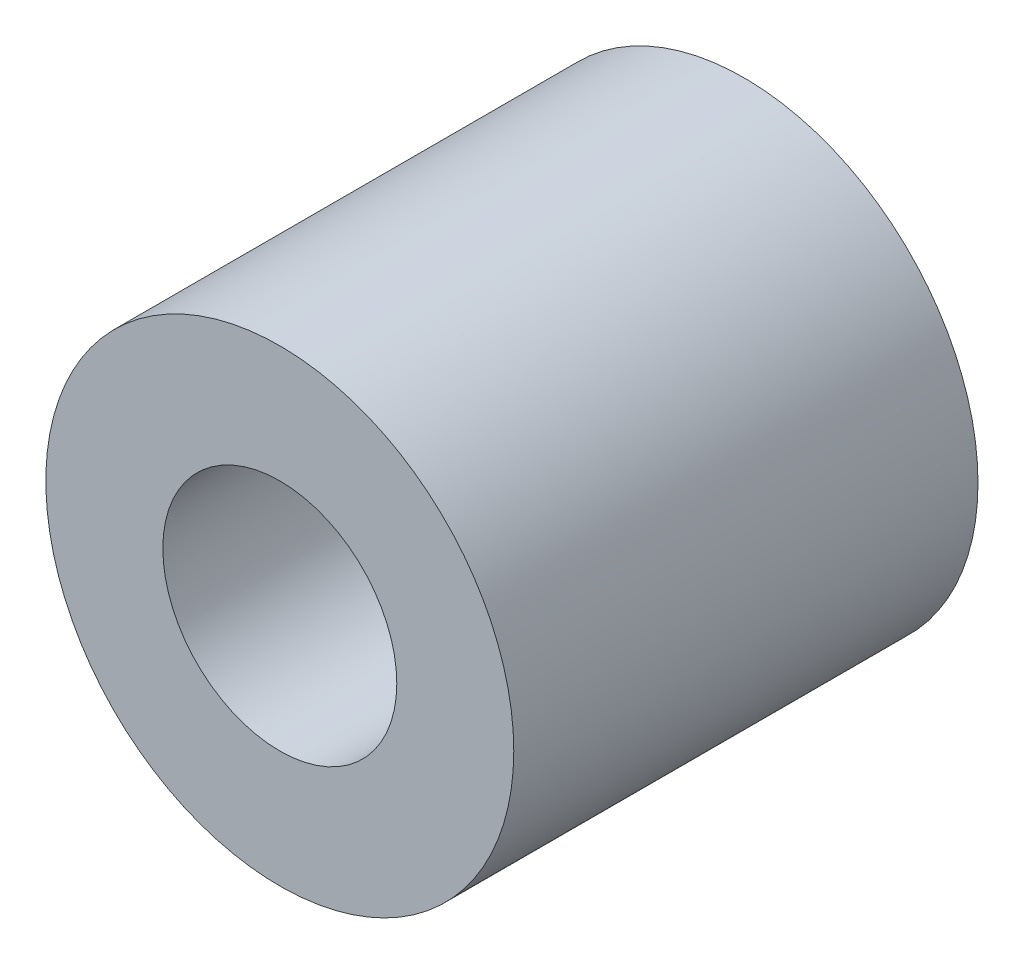
SolidWorks part; units mm, degrees
ref_plane "Front Plane" through (0, 0, 0) normal (0, 0, 1) x (1, 0, 0)
ref_plane "Top Plane" through (0, 0, 0) normal (0, 1, 0) x (1, 0, 0)
ref_plane "Right Plane" through (0, 0, 0) normal (1, 0, 0) x (0, 0, -1)
sketch "Sketch1" plane through (0, 0, 0) normal (0, 0, 1) x (1, 0, 0)
  circle A0 centre (0, 0) radius 3.2004
  circle A1 centre (0, 0) radius 1.6002
  dimension "D1" = 6.4008
  dimension "ID" = 3.2004
extrude "Extrude1" add sketch "Sketch1" along normal mid plane 6.35
sketch "Sketch2" plane through (0, 0, 0) normal (1, 0, 0) x (0, 0, -1)
  line L0 (-3.175, -1.6002) -> (3.175, -1.6002) construction
  line L3 (3.175, 1.6002) -> (-3.175, 1.6002) construction
  line L5 (-3.175, -1.6002) -> (3.175, -1.6002)
  line L6 (3.175, 1.6002) -> (-3.175, 1.6002)
sketch "Sketch4" plane through (0, 0, 3.175) normal (0, 0, 1) x (1, 0, 0)
  line L0 (0, 0) -> (-1.1315, 1.1315)
  line L1 (0, -3.4925) -> (0, 3.4925) construction
  circle A0 centre (0, 0) radius 1.6002 construction
  dimension "D1" = 45
